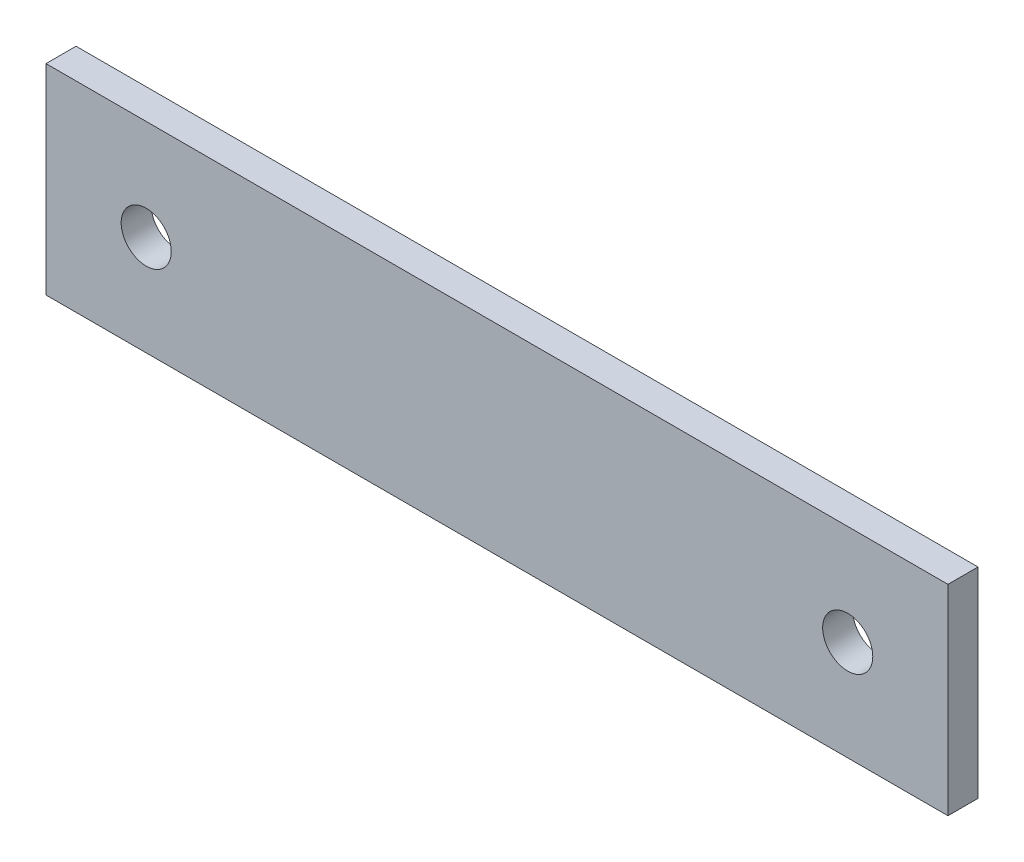
SolidWorks part; units mm, degrees
ref_plane "Front" through (0, 0, 0) normal (0, 0, 1) x (1, 0, 0)
ref_plane "Top" through (0, 0, 0) normal (0, 1, 0) x (1, 0, 0)
ref_plane "Right" through (0, 0, 0) normal (1, 0, 0) x (0, 0, -1)
sketch "Sketch1" plane through (0, 0, 0) normal (0, 0, 1) x (1, 0, 0)
  line L1 (0, 0) -> (90, 0)
  line L2 (0, 0) -> (0, 20)
  line L3 (0, 20) -> (90, 20)
  line L4 (90, 0) -> (90, 20)
  circle A0 centre (10, 10) radius 2.5
  circle A1 centre (80, 10) radius 2.5
  point P9 (0, 10)
  dimension "D3" = 5
  dimension "D4" = 5
  dimension "D1" = 20
  dimension "D2" = 90
  dimension "D5" = 10
  dimension "D6" = 10
extrude "Boss-Extrude1" add sketch "Sketch1" along normal blind 3
equation "\"D4@Sketch1\"=\"D3@Sketch1\""
equation "\"D6@Sketch1\"=\"D5@Sketch1\""
